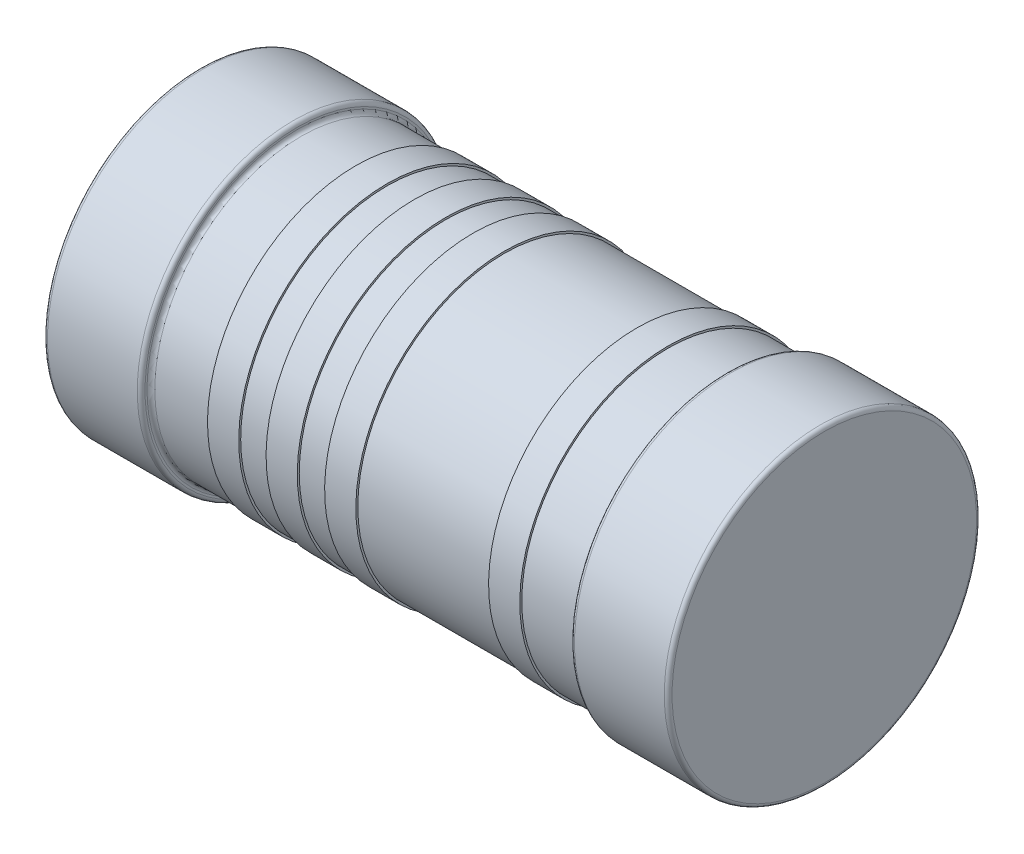
SolidWorks part; units mm, degrees
ref_plane "Front Plane" through (0, 0, 0) normal (0, 0, 1) x (1, 0, 0)
ref_plane "Top Plane" through (0, 0, 0) normal (0, 1, 0) x (1, 0, 0)
ref_plane "Right Plane" through (0, 0, 0) normal (1, 0, 0) x (0, 0, -1)
sketch "Sketch1" plane through (0, 0, 0) normal (0, 0, 1) x (1, 0, 0)
  line L0 (-1.6, 0.8) -> (1.6, 0.8)
  line L1 (0, 0) -> (0, 0.8) construction
  line L2 (-1.6, 0.8) -> (-3.0256, 0.8) construction
  line L3 (1.6, 0.8) -> (1.6, 0.02)
  line L4 (-1.58, 0) -> (-1.12, 0)
  line L5 (-1.6, 0.02) -> (-1.6, 0.8)
  line L6 (-1.1, 0.02) -> (-1.1, 0.03)
  line L7 (-1.08, 0.05) -> (-0.8, 0.05)
  line L8 (1.1, 0.03) -> (1.1, 0.02)
  line L9 (1.12, 0) -> (1.58, 0)
  line L10 (-0.8, 0.05) -> (-0.8, 0.04)
  line L11 (-0.8, 0.04) -> (-0.64, 0.04)
  line L12 (-0.64, 0.04) -> (-0.64, 0.05)
  line L13 (-0.5, 0.05) -> (-0.5, 0.04)
  line L14 (-0.5, 0.04) -> (-0.34, 0.04)
  line L15 (-0.34, 0.04) -> (-0.34, 0.05)
  line L16 (-0.04, 0.04) -> (-0.2, 0.04)
  line L17 (-0.2, 0.04) -> (-0.2, 0.05)
  line L18 (0.8, 0.05) -> (1.08, 0.05)
  line L19 (-0.04, 0.04) -> (-0.04, 0.05)
  line L20 (0.8, 0.05) -> (0.8, 0.04)
  line L21 (0.8, 0.04) -> (0.64, 0.04)
  line L22 (0.64, 0.04) -> (0.64, 0.05)
  line L23 (-0.72, 0.04) -> (-0.72, -0.0114) construction
  line L24 (-0.42, 0.04) -> (-0.42, -0.0114) construction
  line L25 (-0.12, 0.04) -> (-0.12, -0.0151) construction
  line L26 (0.72, 0.04) -> (0.72, -0.0151) construction
  line L27 (-0.04, 0.05) -> (0.64, 0.05)
  line L28 (-0.34, 0.05) -> (-0.2, 0.05)
  line L29 (-0.64, 0.05) -> (-0.5, 0.05)
  arc A0 (1.6, 0.02) -> (1.58, 0) centre (1.58, 0.02) cw
  arc A1 (1.12, 0) -> (1.1, 0.02) centre (1.12, 0.02) cw
  arc A2 (1.1, 0.03) -> (1.08, 0.05) centre (1.08, 0.03) ccw
  arc A3 (-1.08, 0.05) -> (-1.1, 0.03) centre (-1.08, 0.03) ccw
  arc A4 (-1.1, 0.02) -> (-1.12, 0) centre (-1.12, 0.02) cw
  arc A5 (-1.6, 0.02) -> (-1.58, 0) centre (-1.58, 0.02) ccw
  point P15 (1.6, 0)
  point P18 (1.1, 0)
  dimension "D5" = 0.02
  dimension "D1" = 3.2
  dimension "D2" = 0.5
  dimension "D3" = 0.05
  dimension "D4" = 0.8
  dimension "D6" = 0.16
  dimension "D7" = 0.01
  dimension "D8" = 0.3
  dimension "D9" = 0.3
  dimension "D10" = 0.12
  dimension "D11" = 0.72
revolve "Revolve1" add sketch "Sketch1" angle 360 about L2
